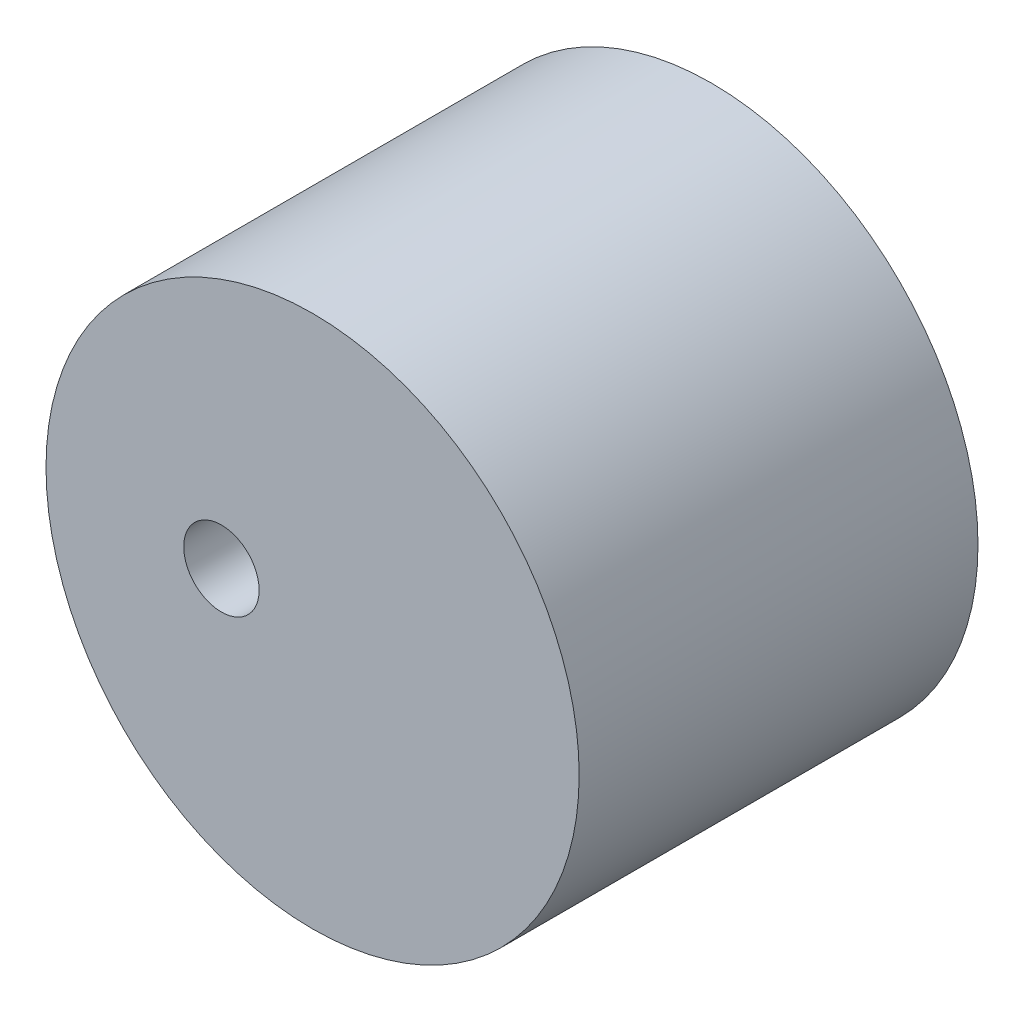
SolidWorks part; units mm, degrees
ref_plane "Front Plane" through (0, 0, 0) normal (0, 0, 1) x (1, 0, 0)
ref_plane "Top Plane" through (0, 0, 0) normal (0, 1, 0) x (1, 0, 0)
ref_plane "Right Plane" through (0, 0, 0) normal (1, 0, 0) x (0, 0, -1)
sketch "Sketch11" plane through (0, 0, 0) normal (0, 0, 1) x (1, 0, 0)
  circle A0 centre (0, 0) radius 23.3938
  circle A1 centre (-8, 0) radius 3.3085
  point P4 (0, 0)
extrude "Boss-Extrude13" add sketch "Sketch11" along normal blind 35
